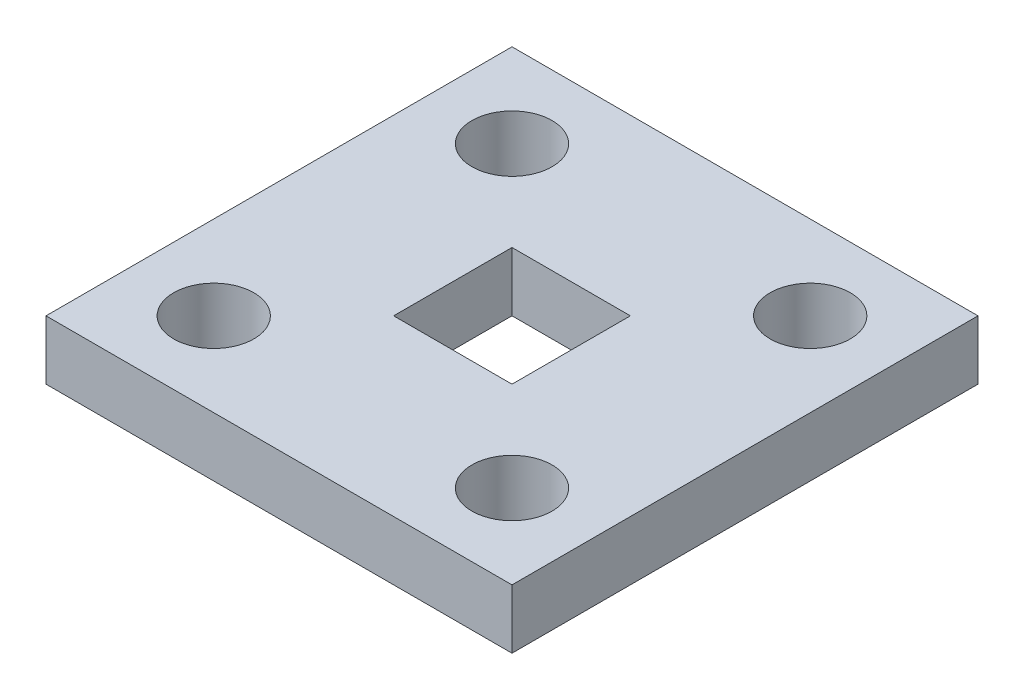
SolidWorks part; units mm, degrees
ref_plane "Front Plane" through (0, 0, 0) normal (0, 0, 1) x (1, 0, 0)
ref_plane "Top Plane" through (0, 0, 0) normal (0, 1, 0) x (1, 0, 0)
ref_plane "Right Plane" through (0, 0, 0) normal (1, 0, 0) x (0, 0, -1)
sketch "Sketch1" plane through (0, 0, 0) normal (0, 1, 0) x (1, 0, 0)
  line L1 (-12.5, -12.5) -> (12.5, -12.5)
  line L2 (-12.5, -12.5) -> (-12.5, 12.5)
  line L3 (-12.5, 12.5) -> (12.5, 12.5)
  line L4 (12.5, -12.5) -> (12.5, 12.5)
  line L5 (-12.5, -12.5) -> (12.5, 12.5) construction
  line L6 (-12.5, 12.5) -> (12.5, -12.5) construction
  line L7 (-8, -8) -> (8, -8) construction
  line L8 (-8, -8) -> (-8, 8) construction
  line L9 (-8, 8) -> (8, 8) construction
  line L10 (8, -8) -> (8, 8) construction
  line L11 (-8, -8) -> (8, 8) construction
  line L12 (-8, 8) -> (8, -8) construction
  line L13 (-3.175, -3.175) -> (3.175, -3.175)
  line L14 (-3.175, -3.175) -> (-3.175, 3.175)
  line L15 (-3.175, 3.175) -> (3.175, 3.175)
  line L16 (3.175, -3.175) -> (3.175, 3.175)
  line L17 (-3.175, -3.175) -> (3.175, 3.175) construction
  line L18 (-3.175, 3.175) -> (3.175, -3.175) construction
  circle A0 centre (-8, 8) radius 2.15
  circle A1 centre (8, 8) radius 2.15
  circle A2 centre (8, -8) radius 2.15
  circle A3 centre (-8, -8) radius 2.15
  point P0 (0, 0)
  point P6 (0, 0)
  point P11 (0, 0)
  point P20 (-8, -8)
  dimension "D4" = 4.3
  dimension "D1" = 6.35
  dimension "D2" = 16
  dimension "D3" = 25
extrude "Boss-Extrude1" add sketch "Sketch1" along normal blind 3.175
